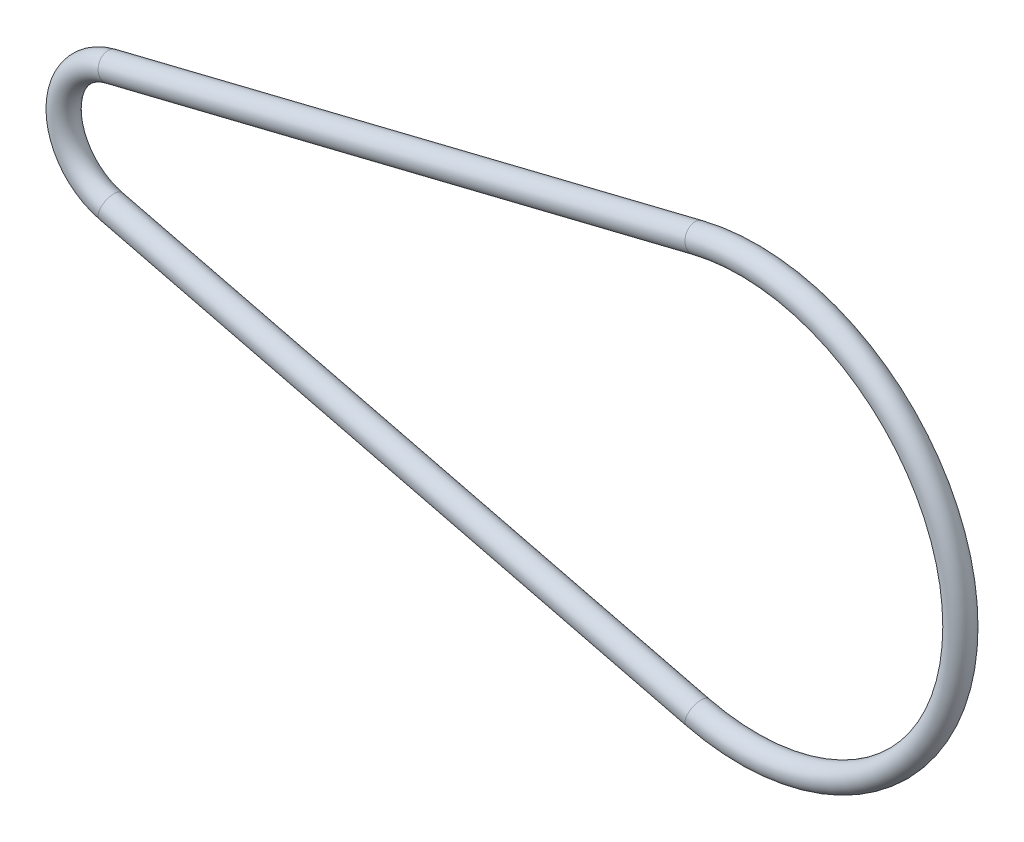
SolidWorks part; units mm, degrees
material "NEOPRENE"
ref_plane "Front Plane" through (0, 0, 0) normal (0, 0, 1) x (1, 0, 0)
ref_plane "Top Plane" through (0, 0, 0) normal (0, 1, 0) x (1, 0, 0)
ref_plane "Right Plane" through (0, 0, 0) normal (1, 0, 0) x (0, 0, -1)
sketch "Sketch1" plane through (0, 0, 0) normal (0, 0, 1) x (1, 0, 0)
  line L0 (-1.2, 4.8539) -> (45.92, 16.5031)
  line L1 (45.92, -16.5031) -> (-1.2, -4.8539)
  arc A0 (-1.2, 4.8539) -> (-1.2, -4.8539) centre (0, 0) ccw
  arc A1 (45.92, 16.5031) -> (45.92, -16.5031) centre (50, 0) cw
  dimension "D1" = 5
  dimension "D2" = 17
  dimension "D3" = 50
sweep "Sweep1" add path "Sketch1" circular profile diameter 2 parameters "D3"=2
